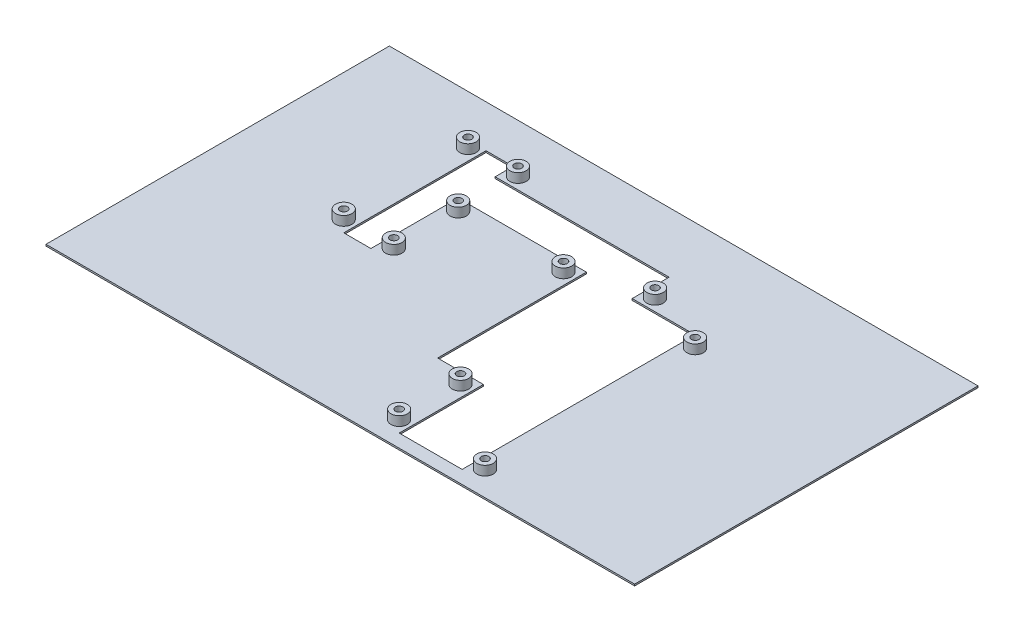
SolidWorks part; units mm, degrees
ref_plane "Front Plane" through (0, 0, 0) normal (0, 0, 1) x (1, 0, 0)
ref_plane "Top Plane" through (0, 0, 0) normal (0, 1, 0) x (1, 0, 0)
ref_plane "Right Plane" through (0, 0, 0) normal (1, 0, 0) x (0, 0, -1)
sketch "Sketch1" plane through (0, 0, 0) normal (0, 1, 0) x (1, 0, 0)
  line L4 (-201.4937, 0) -> (229.5472, 0) construction
  line L5 (0, -45.5) -> (28, -45.5)
  line L10 (0, 185.7213) -> (0, -147.4824) construction
  line L11 (180, 105) -> (-180, -105) construction
  line L16 (180, -105) -> (-180, 105) construction
  line L17 (28, -97) -> (28, -45.5)
  line L19 (66.5, -97) -> (66.5, -45.5)
  line L20 (66.5, -97) -> (28, -97)
  line L21 (-180, -105) -> (-180, 105)
  line L22 (180, 105) -> (-180, 105)
  line L23 (180, -105) -> (180, 105)
  line L24 (180, -105) -> (-180, -105)
  line L25 (0, -45.5) -> (0, 45.5)
  line L26 (28, 45.5) -> (66.5, 45.5)
  line L27 (66.5, -45.5) -> (66.5, 45.5)
  line L36 (-78.4, 68.1) -> (-78.4, 79.1)
  line L37 (-95, -7.9) -> (-78.4, -7.9)
  line L38 (-95, -7.9) -> (-95, 79.1)
  line L39 (-95, 79.1) -> (-78.4, 79.1)
  line L40 (-78.4, -7.9) -> (-78.4, 45.7333)
  line L41 (-78.4, 68.1) -> (28, 68.1)
  line L42 (-78.4, 45.7333) -> (-78.4, 45.5)
  line L43 (-78.4, 45.5) -> (0, 45.5)
  line L48 (28, 45.5) -> (28, 68.1)
  line L51 (-86.7824, 0) -> (-86.7, 79.1) construction
  point P0 (0, 0)
  point P3 (0, 0)
  point P5 (0, 0)
  point P22 (0, 0)
  dimension "D1" = 210
  dimension "D2" = 360
  dimension "D3" = 66.5
  dimension "D4" = 91
  dimension "D5" = 208
  dimension "D6" = 8
  dimension "D7" = 85
  dimension "D9" = 16.6
  dimension "D10" = 87
  dimension "D11" = 28
  dimension "D12" = 11
  dimension "D13" = 22.6
extrude "Boss-Extrude1" add sketch "Sketch1" along normal blind 1 contours L24 L23 L22 L21 L48 L26 L27 L19 L20 L17 L5 L25 L43 L40 L37 L38 L39 L36 L41
sketch "Sketch2" plane through (0, 1, 0) normal (0, 1, 0) x (1, 0, 0)
  line L0 (-106.8643, -7.9) -> (-39.2074, -7.9) construction
  line L1 (-78.4, 68.1) -> (28, 68.1) construction
  line L2 (-95, -7.9) -> (-95, 79.1) construction
  line L3 (-78.4, 68.1) -> (-78.4, 79.1) construction
  line L4 (-59.493, 75.1) -> (-110.149, 75.1) construction
  line L5 (-78.4, 45.5) -> (0, 45.5) construction
  line L6 (-78.4, -7.9) -> (-78.4, 45.5) construction
  line L7 (28, 45.5) -> (28, 68.1) construction
  line L8 (28, 45.5) -> (66.5, 45.5) construction
  line L9 (-95, -7.9) -> (-78.4, -7.9) construction
  line L10 (0, -45.5) -> (0, 45.5) construction
  line L11 (28, 45.5) -> (123.4571, 45.5) construction
  line L12 (66.5, -97) -> (66.5, 45.5) construction
  line L13 (28, -97) -> (28, -45.5) construction
  line L14 (0, -45.5) -> (28, -45.5) construction
  line L15 (0, -97) -> (93.983, -97) construction
  line L16 (66.5, -97) -> (28, -97) construction
  circle A1 centre (-71.4, 75.1) radius 7 construction
  circle A2 centre (-71.4, 75.1) radius 5
  circle A3 centre (-71.4, 75.1) radius 2.3
  circle A7 centre (-71.4, 38.5) radius 7 construction
  circle A8 centre (-71.4, 38.5) radius 5
  circle A9 centre (-71.4, 38.5) radius 2.3
  circle A10 centre (-102, 75.1) radius 7 construction
  circle A11 centre (-102, 75.1) radius 5
  circle A12 centre (-102, 75.1) radius 2.3
  circle A13 centre (-7, 38.5) radius 7 construction
  circle A14 centre (-7, 38.5) radius 5
  circle A15 centre (-7, 38.5) radius 2.3
  circle A16 centre (35, 52.5) radius 7 construction
  circle A17 centre (35, 52.5) radius 5
  circle A18 centre (35, 52.5) radius 2.3
  circle A19 centre (21, -52.5) radius 7 construction
  circle A20 centre (21, -52.5) radius 5
  circle A21 centre (21, -52.5) radius 2.3
  circle A22 centre (-71.4, -0.9) radius 7 construction
  circle A23 centre (-71.4, -0.9) radius 5
  circle A24 centre (-71.4, -0.9) radius 2.3
  circle A25 centre (-102, -0.9) radius 7 construction
  circle A26 centre (-102, -0.9) radius 5
  circle A27 centre (-102, -0.9) radius 2.3
  circle A28 centre (73.5, 38.5) radius 7 construction
  circle A29 centre (73.5, 38.5) radius 5
  circle A30 centre (73.5, 38.5) radius 2.3
  circle A31 centre (73.5, -90) radius 7 construction
  circle A32 centre (73.5, -90) radius 5
  circle A33 centre (73.5, -90) radius 2.3
  circle A34 centre (21, -90) radius 7 construction
  circle A35 centre (21, -90) radius 5
  circle A36 centre (21, -90) radius 2.3
  dimension "D1" = 14
  dimension "D2" = 10
  dimension "D3" = 4.6
  dimension "D4" = 14
  dimension "D5" = 10
  dimension "D6" = 4.6
  dimension "D7" = 14
  dimension "D8" = 10
  dimension "D9" = 4.6
  dimension "D10" = 14
  dimension "D11" = 10
  dimension "D12" = 4.6
  dimension "D13" = 14
  dimension "D14" = 10
  dimension "D15" = 4.6
  dimension "D16" = 14
  dimension "D17" = 10
  dimension "D18" = 4.6
  dimension "D19" = 14
  dimension "D20" = 10
  dimension "D21" = 4.6
  dimension "D22" = 14
  dimension "D23" = 10
  dimension "D24" = 4.6
  dimension "D25" = 14
  dimension "D26" = 10
  dimension "D27" = 4.6
  dimension "D28" = 14
  dimension "D29" = 10
  dimension "D30" = 4.6
  dimension "D31" = 14
  dimension "D32" = 10
  dimension "D33" = 4.6
extrude "Boss-Extrude2" add sketch "Sketch2" along normal blind 5.7 from surface at 0 starting at face at (-18.4714, 1, -12.5429)
